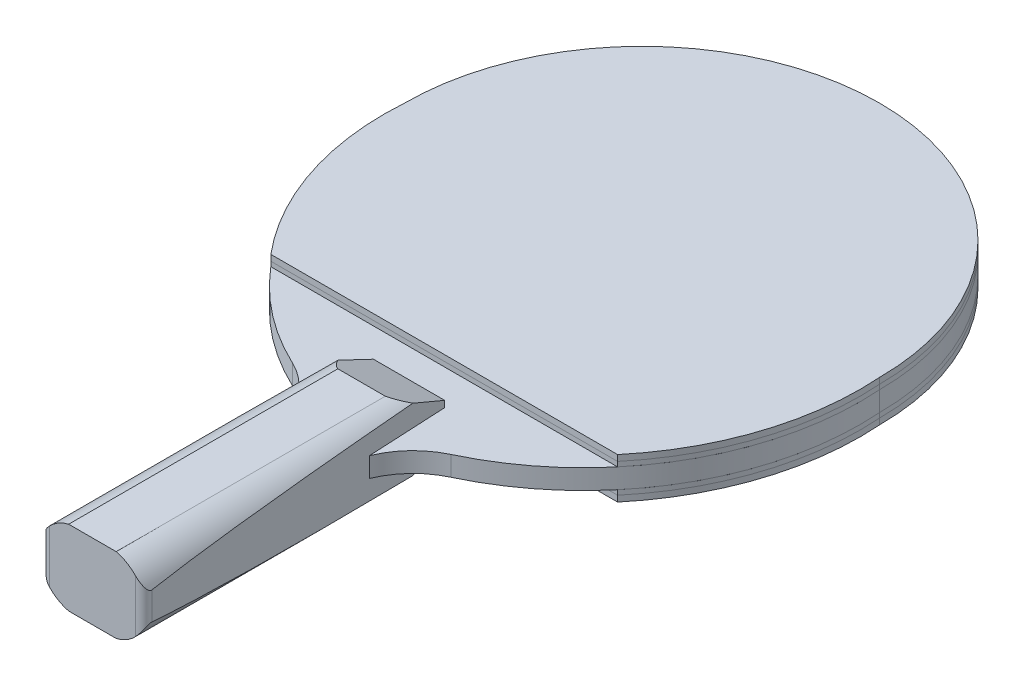
SolidWorks part; units mm, degrees
material "Beech"
ref_plane "Front Plane" through (0, 0, 0) normal (0, 0, 1) x (1, 0, 0)
ref_plane "Top Plane" through (0, 0, 0) normal (0, 1, 0) x (1, 0, 0)
ref_plane "Right Plane" through (0, 0, 0) normal (1, 0, 0) x (0, 0, -1)
sketch "Sketch2" plane through (0, 0, 0) normal (0, 1, 0) x (1, 0, 0)
  line L0 (0, -1000) -> (0, 49000) construction
  line L1 (-12.7, -100.1709) -> (-16.3767, -173.7041)
  line L2 (-13.8398, -176.3709) -> (13.8398, -176.3709)
  line L3 (12.7, -100.1709) -> (16.3767, -173.7041)
  arc A0 (-76.2, 0) -> (76.2, 0) centre (0, 0) cw
  arc A1 (76.2, 0) -> (25.4, -86.7792) centre (-12.4729, -6.35) cw
  arc A2 (-76.2, 0) -> (-25.4, -86.7792) centre (12.4729, -6.35) ccw
  arc A3 (25.4, -86.7792) -> (12.7, -100.1709) centre (36.2208, -109.7589) ccw
  arc A4 (-25.4, -86.7792) -> (-12.7, -100.1709) centre (-36.2208, -109.7589) cw
  arc A5 (-16.3767, -173.7041) -> (-13.8398, -176.3709) centre (-13.8398, -173.8309) ccw
  arc A6 (16.3767, -173.7041) -> (13.8398, -176.3709) centre (13.8398, -173.8309) cw
  point P17 (0, -176.3709)
  point P19 (-16.51, -176.3709)
  point P22 (16.51, -176.3709)
  dimension "D1" = 76.2
  dimension "D3" = 88.9
  dimension "D6" = 25.4
  dimension "D9" = 2.54
  dimension "D2" = 50.8
  dimension "D4" = 6.35
  dimension "D5" = 25.4
  dimension "D7" = 76.2
  dimension "D8" = 16.51
extrude "Boss-Extrude1" add sketch "Sketch2" along normal blind 6.35
sketch "Sketch3" plane through (0, 6.35, 0) normal (0, 1, 0) x (1, 0, 0)
  line L0 (-55.6232, -63.5) -> (55.6232, -63.5)
  arc A0 (76.2, 0) -> (-76.2, 0) centre (0, 0) ccw construction
  arc A1 (-76.2, 0) -> (-25.4, -86.7792) centre (12.4729, -6.35) ccw construction
  arc A2 (25.4, -86.7792) -> (76.2, 0) centre (-12.4729, -6.35) ccw construction
  arc A3 (76.2, 0) -> (-76.2, 0) centre (0, 0) ccw
  arc A4 (-76.2, 0) -> (-55.6232, -63.5) centre (12.4729, -6.35) ccw
  arc A5 (55.6232, -63.5) -> (76.2, 0) centre (-12.4729, -6.35) ccw
  dimension "D1" = 63.5
extrude "Boss-Extrude2" add sketch "Sketch3" along normal blind 1.524 separate body
sketch "Sketch4" plane through (0, 7.874, 0) normal (0, 1, 0) x (1, 0, 0)
  line L0 (-55.6232, -63.5) -> (55.6232, -63.5) construction
  line L1 (-55.6232, -63.5) -> (55.6232, -63.5)
  arc A0 (-76.2, 0) -> (-55.6232, -63.5) centre (12.4729, -6.35) ccw construction
  arc A1 (76.2, 0) -> (-76.2, 0) centre (0, 0) ccw construction
  arc A2 (55.6232, -63.5) -> (76.2, 0) centre (-12.4729, -6.35) ccw construction
  arc A3 (-76.2, 0) -> (-55.6232, -63.5) centre (12.4729, -6.35) ccw
  arc A4 (76.2, 0) -> (-76.2, 0) centre (0, 0) ccw
  arc A5 (55.6232, -63.5) -> (76.2, 0) centre (-12.4729, -6.35) ccw
extrude "Boss-Extrude4" add sketch "Sketch4" along normal blind 1.905 separate body
ref_plane "Plane1" through (0, 3.175, 0) normal (0, 1, 0) x (1, 0, 0)
sketch "Sketch5" plane through (0, 0, 0) normal (0, -1, 0) x (1, 0, 0)
  line L0 (55.6232, 63.5) -> (-55.6232, 63.5)
  line L3 (12.7, 100.1709) -> (16.3767, 173.7041)
  line L4 (13.8398, 176.3709) -> (-13.8398, 176.3709)
  line L5 (-16.3767, 173.7041) -> (-12.7, 100.1709)
  arc A7 (-25.4, 86.7792) -> (-76.2, 0) centre (12.4729, 6.35) ccw
  arc A8 (-76.2, 0) -> (76.2, 0) centre (0, 0) ccw
  arc A9 (76.2, 0) -> (25.4, 86.7792) centre (-12.4729, 6.35) ccw
  arc A10 (12.7, 100.1709) -> (25.4, 86.7792) centre (36.2208, 109.7589) ccw
  arc A11 (16.3767, 173.7041) -> (13.8398, 176.3709) centre (13.8398, 173.8309) ccw
  arc A12 (-13.8398, 176.3709) -> (-16.3767, 173.7041) centre (-13.8398, 173.8309) ccw
  arc A13 (-25.4, 86.7792) -> (-12.7, 100.1709) centre (-36.2208, 109.7589) ccw
  arc A14 (-55.6232, 63.5) -> (-76.2, 0) centre (12.4729, 6.35) ccw
  arc A15 (-76.2, 0) -> (76.2, 0) centre (0, 0) ccw
  arc A16 (76.2, 0) -> (55.6232, 63.5) centre (-12.4729, 6.35) ccw
  dimension "D2" = 63.5
  dimension "D1" = 0
extrude "Boss-Extrude5" add sketch "Sketch5" along normal blind 1.524 separate body
sketch "Sketch6" plane through (0, -1.524, 0) normal (0, -1, 0) x (1, 0, 0)
  line L1 (55.6232, 63.5) -> (-55.6232, 63.5)
  line L2 (55.6232, 63.5) -> (-55.6232, 63.5)
  arc A3 (76.2, 0) -> (55.6232, 63.5) centre (-12.4729, 6.35) ccw
  arc A4 (-55.6232, 63.5) -> (-76.2, 0) centre (12.4729, 6.35) ccw
  arc A5 (-76.2, 0) -> (76.2, 0) centre (0, 0) ccw
  arc A6 (76.2, 0) -> (55.6232, 63.5) centre (-12.4729, 6.35) ccw
  arc A7 (-55.6232, 63.5) -> (-76.2, 0) centre (12.4729, 6.35) ccw
  arc A8 (-76.2, 0) -> (76.2, 0) centre (0, 0) ccw
  dimension "D1" = 0
extrude "Boss-Extrude6" add sketch "Sketch6" along normal blind 1.905 separate body
sketch "Sketch7" plane through (0, 6.35, 0) normal (0, 1, 0) x (1, 0, 0)
  line L0 (-12.7, -100.1709) -> (-16.3767, -173.7041) construction
  line L1 (16.3767, -173.7041) -> (12.7, -100.1709) construction
  line L2 (-13.8398, -176.3709) -> (13.8398, -176.3709) construction
  line L3 (-11.43, -74.7709) -> (-16.3767, -173.7041)
  line L4 (16.3767, -173.7041) -> (11.43, -74.7709)
  line L5 (-13.8398, -176.3709) -> (13.8398, -176.3709)
  line L6 (-11.43, -74.7709) -> (11.43, -74.7709)
  arc A0 (13.8398, -176.3709) -> (16.3767, -173.7041) centre (13.8398, -173.8309) ccw construction
  arc A1 (-16.3767, -173.7041) -> (-13.8398, -176.3709) centre (-13.8398, -173.8309) ccw construction
  arc A2 (13.8398, -176.3709) -> (16.3767, -173.7041) centre (13.8398, -173.8309) ccw
  arc A3 (-16.3767, -173.7041) -> (-13.8398, -176.3709) centre (-13.8398, -173.8309) ccw
  dimension "D1" = 101.6
extrude "Boss-Extrude7" add sketch "Sketch7" along normal blind 8.89
sketch "Sketch8" plane through (0, 0, 176.3709) normal (0, 0, 1) x (1, 0, 0)
  line L0 (-16.3798, 15.24) -> (-16.3798, 0) construction
  line L1 (-13.8398, 15.24) -> (13.8398, 15.24) construction
  line L2 (16.3798, 0) -> (16.3798, 15.24) construction
  line L4 (0, -1000) -> (0, 15.24) construction
  line L5 (16.3798, 15.24) -> (13.8398, 15.24) construction
  line L6 (-13.8398, 15.24) -> (-16.3798, 15.24) construction
  line L7 (-13.8398, 15.24) -> (-7.62, 15.24)
  line L8 (16.3798, 15.24) -> (13.8398, 15.24)
  line L9 (16.3798, 7.62) -> (16.3798, 15.24)
  line L10 (-13.8398, 15.24) -> (-16.3798, 15.24)
  line L11 (-16.3798, 15.24) -> (-16.3798, 7.62)
  line L12 (7.62, 15.24) -> (13.8398, 15.24)
  arc A0 (-16.3798, 7.62) -> (-7.62, 15.24) centre (-4.5865, 2.9076) cw
  arc A1 (16.3798, 7.62) -> (7.62, 15.24) centre (4.5865, 2.9076) ccw
  dimension "D2" = 12.7
  dimension "D3" = 12.7
  dimension "D1" = 15.24
extrude "Cut-Extrude1" cut sketch "Sketch8" against normal blind 101.6
sketch "Sketch9" plane through (0, 0, -0.1919) normal (1, 0, 0) x (0, 0, -1)
  line L0 (-74.9628, 8.382) -> (-90.2028, 15.24)
  line L1 (-74.9628, 13.606) -> (-74.9628, 6.35) construction
  line L2 (-74.9628, 15.24) -> (-176.5628, 15.24) construction
  line L3 (-90.2028, 15.24) -> (-74.9628, 15.24)
  line L4 (-74.9628, 15.24) -> (-74.9628, 8.382)
  dimension "D1" = 15.24
  dimension "D2" = 15.24
  dimension "D3" = 6.858
extrude "Cut-Extrude2" cut sketch "Sketch9" against normal mid plane 50.8
mirror "Mirror8" about plane through (0, 3.175, 0) normal (0, 1, 0) of "Boss-Extrude7", "Cut-Extrude1", "Cut-Extrude2"
